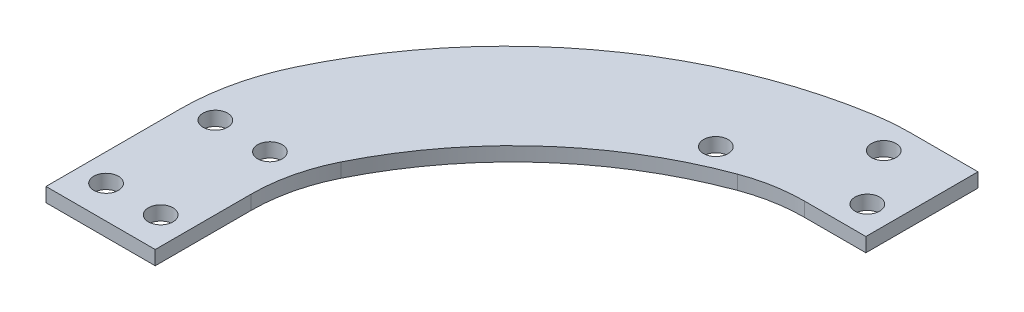
SolidWorks part; units mm, degrees
ref_plane "Front Plane" through (0, 0, 0) normal (0, 0, 1) x (1, 0, 0)
ref_plane "Top Plane" through (0, 0, 0) normal (0, 1, 0) x (1, 0, 0)
ref_plane "Right Plane" through (0, 0, 0) normal (1, 0, 0) x (0, 0, -1)
sketch "Sketch1" plane through (0, 0, 0) normal (0, 1, 0) x (1, 0, 0)
  line L0 (10, -16) -> (73, -16) construction
  line L1 (-10, -16) -> (10, -16)
  line L2 (-10, -16) -> (-10, 8.5279)
  line L3 (-10, 16) -> (10, 16)
  line L4 (10, -16) -> (10, 1.5711)
  line L5 (-10, -16) -> (10, 16) construction
  line L6 (-10, 16) -> (10, -16) construction
  line L7 (73, -16) -> (73, 51.12) construction
  line L8 (73, 51.12) -> (73, 71.65)
  line L9 (73, 51.12) -> (61.745, 51.12)
  line L10 (73, 71.65) -> (60.7297, 71.65)
  line L11 (58, 51.12) -> (58, 71.65)
  arc A0 (13.1197, 14.8922) -> (51.3501, 49.2615) centre (75.4563, -16) cw
  arc A1 (-6.1158, 25.7223) -> (54.2128, 71.1155) centre (67.4957, -9.3234) cw
  arc A2 (10, 1.5711) -> (13.1197, 14.8922) centre (40, 1.5711) cw
  arc A3 (51.3501, 49.2615) -> (61.745, 51.12) centre (61.745, 21.12) cw
  arc A4 (-6.1158, 25.7223) -> (-10, 8.5279) centre (30, 8.5279) ccw
  arc A5 (60.7297, 71.65) -> (54.2128, 71.1155) centre (60.7297, 31.65) ccw
  point P0 (0, 0)
  dimension "D2" = 30
  dimension "D7" = 40
  dimension "D1" = 32
  dimension "D3" = 67.12
  dimension "D4" = 63
  dimension "D5" = 20.53
  dimension "D6" = 15
extrude "Boss-Extrude1" add sketch "Sketch1" along normal blind 2.5883
hole_wizard "M4 Clearance Hole1" positions "Sketch2" profile "Sketch3" hole size "M4" standard "ANSI Metric" end condition through all
sketch "Sketch2" plane through (0, 2.5883, 0) normal (0, 1, 0) x (1, 0, 0)
  line L0 (-5, -10) -> (5, 10) construction
  line L2 (-5, -10) -> (5, -10)
  line L4 (-5, 10) -> (5, 10)
  line L6 (-5, 10) -> (-5, -10)
  point P0 (-5, 10)
  point P2 (5, 10)
  point P4 (5, -10)
  point P6 (-5, -10)
  point P26 (0, 0)
  dimension "D1" = 10
  dimension "D2" = 20
sketch "Sketch3" plane through (-5, 2.5883, -10) normal (1, 0, 0) x (0, 0, 1)
  line L0 (0, 0) -> (0, 2.5883)
  line L1 (0, 2.5883) -> (2.25, 2.5883)
  line L2 (2.25, 2.5883) -> (2.25, 0)
  line L5 (2.25, 0) -> (0, 0)
  line L11 (0, -6.35) -> (0, 107.95) construction
  dimension "Thru Hole Dia." = 4.5
  dimension "Thru Hole Depth" = 2.5883
hole_wizard "M4 Clearance Hole2" positions "Sketch4" profile "Sketch5" hole size "M4" standard "ANSI Metric" end condition through all
sketch "Sketch4" plane through (0, 2.5883, 0) normal (0, 1, 0) x (1, 0, 0)
  line L0 (73, 61.385) -> (61.4263, 61.385) construction
  line L1 (73, 51.12) -> (73, 71.65) construction
  line L3 (61, 66.385) -> (68, 56.385) construction
  point P0 (61, 66.385)
  point P2 (68, 56.385)
  point P13 (64.5, 61.385)
  dimension "D1" = 7
  dimension "D2" = 10
  dimension "D3" = 5
sketch "Sketch5" plane through (61, 2.5883, -66.385) normal (1, 0, 0) x (0, 0, 1)
  line L0 (0, 0) -> (0, 2.5883)
  line L1 (0, 2.5883) -> (2.25, 2.5883)
  line L2 (2.25, 2.5883) -> (2.25, 0)
  line L5 (2.25, 0) -> (0, 0)
  line L11 (0, -6.35) -> (0, 107.95) construction
  dimension "Thru Hole Dia." = 4.5
  dimension "Thru Hole Depth" = 2.5883
hole_wizard "M4 Clearance Hole3" positions "Sketch7" profile "Sketch8" hole size "M4" standard "ANSI Metric"
sketch "Sketch7" plane through (0, 0, 0) normal (0, -1, 0) x (-1, 0, 0)
  line L0 (-73, 51.12) -> (-73, 71.65) construction
  line L1 (-73, 71.65) -> (-60.7297, 71.65) construction
  point P0 (-45, 51.65)
  dimension "D1" = 28
  dimension "D2" = 20
sketch "Sketch8" plane through (45, 0, -51.65) normal (1, 0, 0) x (0, 0, -1)
  line L0 (0, 0) -> (0, 13.8019)
  line L1 (0, 13.8019) -> (2.25, 12.45)
  line L2 (2.25, 12.45) -> (2.25, 0)
  line L5 (2.25, 0) -> (0, 0)
  line L10 (0, 13.8019) -> (-2.25, 12.45) construction
  line L11 (0, -6.35) -> (0, 107.95) construction
  dimension "Hole Dia." = 4.5
  dimension "Hole Depth" = 12.45
  dimension "Drill Angle" = 118
